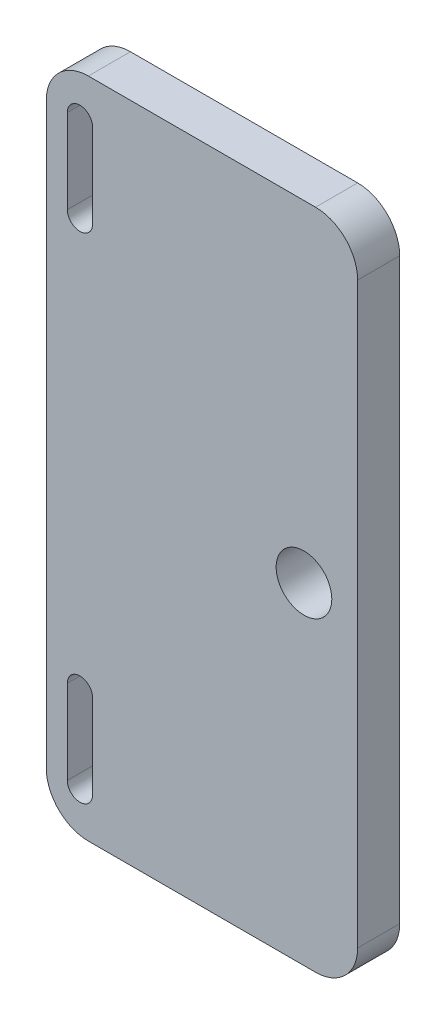
SolidWorks part; units mm, degrees
ref_plane "Front Plane" through (0, 0, 0) normal (0, 0, 1) x (1, 0, 0)
ref_plane "Top Plane" through (0, 0, 0) normal (0, 1, 0) x (1, 0, 0)
ref_plane "Right Plane" through (0, 0, 0) normal (1, 0, 0) x (0, 0, -1)
sketch "Sketch1" plane through (0, 0, 0) normal (0, 0, 1) x (1, 0, 0)
  line L0 (-5.95, 25) -> (-5.95, -25)
  line L1 (20.365, 25) -> (-20.365, 25) construction
  line L2 (-20.365, -25) -> (20.365, -25) construction
  line L3 (-5.95, -25) -> (-25, -25)
  line L4 (-25, -25) -> (-25, 25)
  line L5 (-25, 25) -> (-5.95, 25)
  line L6 (-25, 20.365) -> (-25, 3.35) construction
  circle A0 centre (-10, 0) radius 2.1 construction
  circle A1 centre (-10, 0) radius 2.1
  dimension "D1" = 19.05
extrude "Boss-Extrude1" add sketch "Sketch1" along normal blind 3.175
sketch "Sketch2" plane through (0, 0, 3.175) normal (0, 0, 1) x (1, 0, 0)
  line L0 (-5.95, 25) -> (-25, 25) construction
  line L1 (-25, -25) -> (-29.445, -25)
  line L2 (-25, -25) -> (-25, 25)
  line L3 (-25, 25) -> (-29.445, 25)
  line L4 (-29.445, -25) -> (-29.445, 25)
  dimension "D1" = 4.445
extrude "Boss-Extrude2" add sketch "Sketch2" against normal blind 3.175
sketch "Sketch3" plane through (0, 0, 3.175) normal (0, 0, 1) x (1, 0, 0)
  line L0 (-26.905, -15.475) -> (-26.905, -21.825) construction
  line L1 (-25.9525, -15.475) -> (-25.9525, -21.825)
  line L2 (-27.8575, -15.475) -> (-27.8575, -21.825)
  line L3 (-29.445, 25) -> (-29.445, -25) construction
  line L4 (-29.445, -25) -> (-5.95, -25) construction
  line L5 (-29.445, 0) -> (-10, 0) construction
  line L6 (-18.563, 0) -> (217.6639, 0) construction
  line L7 (-26.905, 15.475) -> (-26.905, 21.825) construction
  line L8 (-25.9525, 15.475) -> (-25.9525, 21.825)
  line L9 (-27.8575, 15.475) -> (-27.8575, 21.825)
  arc A0 (-25.9525, -15.475) -> (-27.8575, -15.475) centre (-26.905, -15.475) ccw
  arc A1 (-27.8575, -21.825) -> (-25.9525, -21.825) centre (-26.905, -21.825) ccw
  arc A2 (-25.9525, 15.475) -> (-27.8575, 15.475) centre (-26.905, 15.475) cw
  arc A3 (-27.8575, 21.825) -> (-25.9525, 21.825) centre (-26.905, 21.825) cw
  point P2 (-26.905, -18.65)
  point P18 (-26.905, 18.65)
  dimension "D1" = 1.905
  dimension "D2" = 2.54
  dimension "D3" = 3.175
  dimension "D4" = 6.35
extrude "Cut-Extrude1" cut sketch "Sketch3" against normal blind 3.175
fillet "Fillet1" radius 3.175 4 edges at (-29.445, -25, 1.5875) (-5.95, -25, 1.5875) (-29.445, 25, 1.5875) (-5.95, 25, 1.5875)
